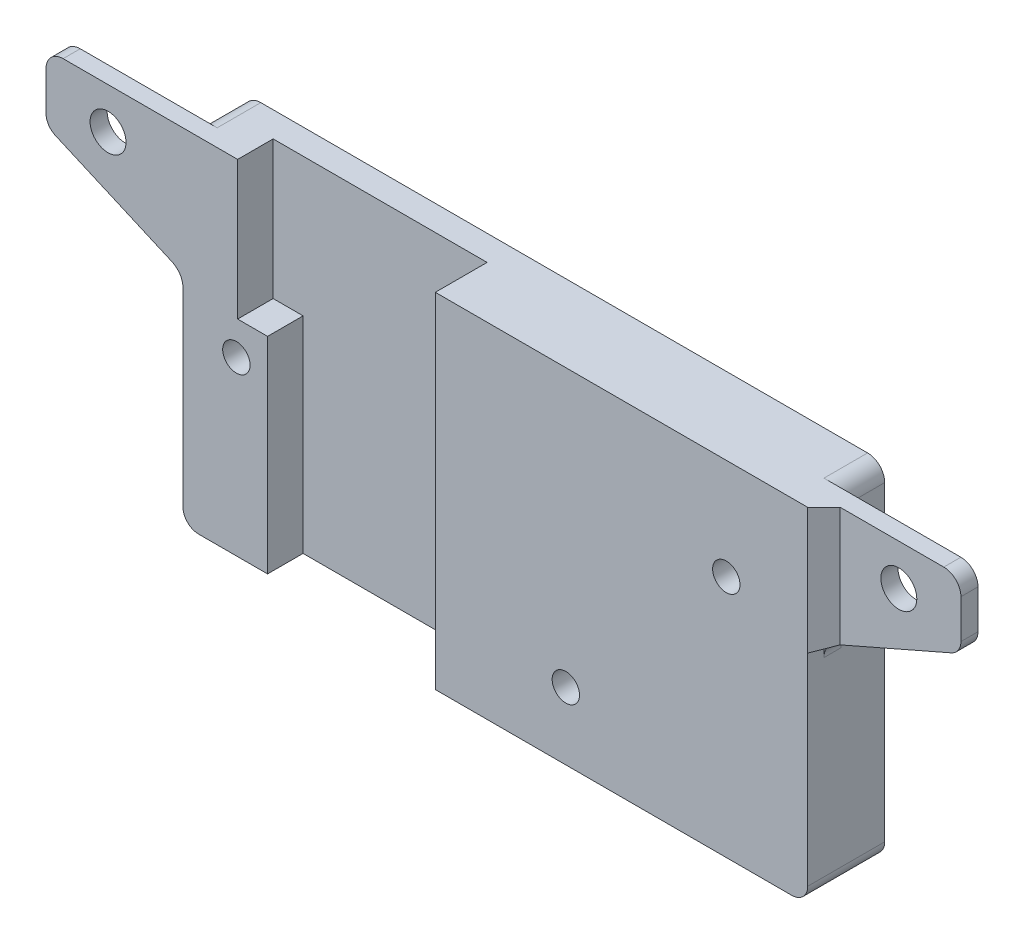
SolidWorks part; units mm, degrees
ref_plane "Front Plane" through (0, 0, 0) normal (0, 0, 1) x (1, 0, 0)
ref_plane "Top Plane" through (0, 0, 0) normal (0, 1, 0) x (1, 0, 0)
ref_plane "Right Plane" through (0, 0, 0) normal (1, 0, 0) x (0, 0, -1)
sketch "Sketch1" plane through (0, 0, 0) normal (0, 0, 1) x (1, 0, 0)
  line L0 (99.95, 149.85) -> (25.05, 149.85)
  line L1 (25.05, 148) -> (25.05, 111.5)
  line L2 (26.9, 109.65) -> (98.1, 109.65)
  line L3 (99.95, 111.5) -> (99.95, 148)
  line L4 (24.9, 148) -> (24.9, 111.5)
  line L5 (26.9, 109.5) -> (98.1, 109.5)
  line L6 (100.1, 111.5) -> (100.1, 148)
  line L7 (102.1, 150) -> (22.9, 150)
  line L8 (24.9, 148) -> (24.9, 111.5) construction
  line L9 (26.9, 109.5) -> (98.1, 109.5) construction
  line L10 (100.1, 111.5) -> (100.1, 148) construction
  line L11 (102.1, 150) -> (22.9, 150) construction
  line L12 (25.05, 148) -> (25.05, 149.85)
  line L14 (101.0046, 149.85) -> (23.9954, 149.85) construction
  line L15 (99.95, 148) -> (99.95, 149.85)
  arc A1 (25.05, 111.5) -> (26.9, 109.65) centre (26.9, 111.5) ccw
  arc A2 (98.1, 109.65) -> (99.95, 111.5) centre (98.1, 111.5) ccw
  arc A4 (24.9, 111.5) -> (26.9, 109.5) centre (26.9, 111.5) ccw
  arc A5 (98.1, 109.5) -> (100.1, 111.5) centre (98.1, 111.5) ccw
  arc A6 (102.1, 150) -> (100.1, 148) centre (102.1, 148) ccw
  arc A7 (24.9, 148) -> (22.9, 150) centre (22.9, 148) ccw
  arc A8 (24.9, 111.5) -> (26.9, 109.5) centre (26.9, 111.5) ccw construction
  arc A9 (98.1, 109.5) -> (100.1, 111.5) centre (98.1, 111.5) ccw construction
  arc A10 (102.1, 150) -> (100.1, 148) centre (102.1, 148) ccw construction
  arc A11 (24.9, 148) -> (22.9, 150) centre (22.9, 148) ccw construction
  arc A16 (25.05, 148) -> (23.9954, 149.85) centre (22.9, 148) ccw construction
  arc A17 (101.0046, 149.85) -> (99.95, 148) centre (102.1, 148) ccw construction
  dimension "D1" = 0
  dimension "D2" = 0.15
extrude "Boss-Extrude1" add sketch "Sketch1" along normal up to surface (5.1 mm away)
sketch "Sketch2" plane through (0, 0, 5.1) normal (0, 0, 1) x (1, 0, 0)
  line L24 (101.2984, 135.5243) -> (114.9016, 141.4757) construction
  line L25 (116.1, 143.308) -> (116.1, 148) construction
  line L26 (118.1, 150) -> (102.1, 150) construction
  line L28 (8.9, 148) -> (8.9, 143.308) construction
  line L29 (10.0984, 141.4757) -> (23.7016, 135.5243) construction
  line L31 (22.9, 150) -> (6.9, 150) construction
  line L32 (101.2984, 135.5243) -> (114.9016, 141.4757) construction
  line L33 (116.1, 143.308) -> (116.1, 148) construction
  line L34 (116.1, 150) -> (102.1, 150) construction
  line L36 (8.9, 148) -> (8.9, 143.308) construction
  line L37 (10.0984, 141.4757) -> (23.7016, 135.5243) construction
  line L39 (22.9, 150) -> (8.9, 150) construction
  line L40 (100.1, 111.5) -> (100.1, 133.692) construction
  line L41 (26.9, 109.5) -> (98.1, 109.5) construction
  line L42 (24.9, 133.692) -> (24.9, 111.5) construction
  line L43 (100.1, 111.5) -> (100.1, 133.692) construction
  line L44 (26.9, 109.5) -> (98.1, 109.5) construction
  line L45 (24.9, 133.692) -> (24.9, 111.5) construction
  line L46 (102.1, 150) -> (22.9, 150) construction
  line L47 (102.1, 150) -> (22.9, 150) construction
  line L48 (8.9, 148) -> (8.9, 150) construction
  line L49 (116.1, 148) -> (116.1, 150) construction
  line L50 (102.1, 149.85) -> (22.9, 149.85)
  line L51 (22.9, 149.85) -> (9.05, 149.85)
  line L52 (9.05, 148) -> (9.05, 149.85)
  line L53 (9.05, 148) -> (9.05, 143.308)
  line L54 (10.1585, 141.6131) -> (23.7618, 135.6617)
  line L55 (25.05, 133.692) -> (25.05, 111.5)
  line L56 (26.9, 109.65) -> (98.1, 109.65)
  line L57 (99.95, 111.5) -> (99.95, 133.692)
  line L58 (101.2382, 135.6617) -> (114.8415, 141.6131)
  line L59 (115.95, 143.308) -> (115.95, 148)
  line L60 (115.95, 148) -> (115.95, 149.85)
  line L61 (115.95, 149.85) -> (102.1, 149.85)
  arc A24 (114.9016, 141.4757) -> (116.1, 143.308) centre (114.1, 143.308) ccw construction
  arc A27 (101.2984, 135.5243) -> (100.1, 133.692) centre (102.1, 133.692) ccw construction
  arc A28 (8.9, 143.308) -> (10.0984, 141.4757) centre (10.9, 143.308) ccw construction
  arc A29 (24.9, 133.692) -> (23.7016, 135.5243) centre (22.9, 133.692) ccw construction
  arc A32 (114.9016, 141.4757) -> (116.1, 143.308) centre (114.1, 143.308) ccw construction
  arc A35 (101.2984, 135.5243) -> (100.1, 133.692) centre (102.1, 133.692) ccw construction
  arc A36 (8.9, 143.308) -> (10.0984, 141.4757) centre (10.9, 143.308) ccw construction
  arc A37 (24.9, 133.692) -> (23.7016, 135.5243) centre (22.9, 133.692) ccw construction
  arc A40 (98.1, 109.5) -> (100.1, 111.5) centre (98.1, 111.5) ccw construction
  arc A41 (24.9, 111.5) -> (26.9, 109.5) centre (26.9, 111.5) ccw construction
  arc A42 (98.1, 109.5) -> (100.1, 111.5) centre (98.1, 111.5) ccw construction
  arc A43 (24.9, 111.5) -> (26.9, 109.5) centre (26.9, 111.5) ccw construction
  arc A44 (9.05, 143.308) -> (10.1585, 141.6131) centre (10.9, 143.308) ccw
  arc A45 (25.05, 133.692) -> (23.7618, 135.6617) centre (22.9, 133.692) ccw
  arc A46 (25.05, 111.5) -> (26.9, 109.65) centre (26.9, 111.5) ccw
  arc A47 (98.1, 109.65) -> (99.95, 111.5) centre (98.1, 111.5) ccw
  arc A48 (101.2382, 135.6617) -> (99.95, 133.692) centre (102.1, 133.692) ccw
  arc A49 (114.8415, 141.6131) -> (115.95, 143.308) centre (114.1, 143.308) ccw
  circle A50 centre (16.3, 145.05) radius 2.1
  circle A51 centre (108.7, 145.05) radius 2.1
  dimension "D2" = 4.2
  dimension "D1" = 0.15
extrude "Boss-Extrude2" add sketch "Sketch2" along normal up to surface (0.9 mm away)
fillet "Fillet1" radius 2 4 edges at (115.95, 149.85, 5.55) (9.05, 149.85, 5.55) (25.05, 149.85, 2.55) (99.95, 149.85, 2.55)
sketch "Sketch3" plane through (0, 0, 6) normal (0, 0, 1) x (1, 0, 0)
  line L0 (99.95, 133.692) -> (99.95, 149.85)
  line L1 (11.05, 149.85) -> (113.95, 149.85) construction
  line L2 (114.8415, 141.6131) -> (101.2382, 135.6617) construction
  line L3 (115.95, 147.85) -> (115.95, 143.308) construction
  line L4 (114.8415, 141.6131) -> (101.2382, 135.6617)
  line L5 (115.95, 147.85) -> (115.95, 143.308)
  line L6 (11.05, 149.85) -> (25.05, 149.85)
  line L7 (25.05, 133.692) -> (25.05, 149.85)
  line L8 (23.7618, 135.6617) -> (10.1585, 141.6131) construction
  line L9 (9.05, 143.308) -> (9.05, 147.85) construction
  line L10 (23.7618, 135.6617) -> (10.1585, 141.6131)
  line L11 (9.05, 143.308) -> (9.05, 147.85)
  line L12 (99.95, 149.85) -> (113.95, 149.85)
  arc A0 (101.2382, 135.6617) -> (99.95, 133.692) centre (102.1, 133.692) ccw construction
  arc A1 (114.8415, 141.6131) -> (115.95, 143.308) centre (114.1, 143.308) ccw construction
  arc A2 (115.95, 147.85) -> (113.95, 149.85) centre (113.95, 147.85) ccw construction
  arc A3 (101.2382, 135.6617) -> (99.95, 133.692) centre (102.1, 133.692) ccw
  arc A4 (114.8415, 141.6131) -> (115.95, 143.308) centre (114.1, 143.308) ccw
  arc A5 (115.95, 147.85) -> (113.95, 149.85) centre (113.95, 147.85) ccw
  arc A6 (25.05, 133.692) -> (23.7618, 135.6617) centre (22.9, 133.692) ccw construction
  arc A7 (9.05, 143.308) -> (10.1585, 141.6131) centre (10.9, 143.308) ccw construction
  arc A8 (11.05, 149.85) -> (9.05, 147.85) centre (11.05, 147.85) ccw construction
  arc A9 (25.05, 133.692) -> (23.7618, 135.6617) centre (22.9, 133.692) ccw
  arc A10 (9.05, 143.308) -> (10.1585, 141.6131) centre (10.9, 143.308) ccw
  arc A11 (11.05, 149.85) -> (9.05, 147.85) centre (11.05, 147.85) ccw
  circle A12 centre (108.7, 145.05) radius 2.1 construction
  circle A13 centre (16.3, 145.05) radius 2.1 construction
  circle A14 centre (108.7, 145.05) radius 2.1
  circle A15 centre (16.3, 145.05) radius 2.1
extrude "Boss-Extrude3" add sketch "Sketch3" along normal offset from surface (1.1 mm away) 2 up to face at (17.4291, 143.8163, 5.1)
sketch "Sketch4" plane through (0, 149.85, 0) normal (0, 1, 0) x (1, 0, 0)
  line L0 (99.95, -7.1) -> (97.45, -6)
  line L1 (25.05, -6) -> (99.95, -6) construction
  line L2 (97.45, -6) -> (99.95, -6)
  line L3 (25.05, -6) -> (25.05, -7.1)
  line L4 (25.05, -7.1) -> (27.55, -6)
  line L5 (27.55, -6) -> (25.05, -6)
  line M6 (25.05, -7.1) -> (25.05, -6)
  line M7 (25.05, -6) -> (99.95, -6)
  line M8 (99.95, -6) -> (99.95, -7.1)
  dimension "D1" = 2.5
extrude "Boss-Extrude4" add sketch "Sketch4" against normal up to vertex (16.158 mm away) contours L4 M6 M7 | L0 M8 M7 up to point (25.05, 133.692, 7.1)
sketch "Sketch5" plane through (0, 0, 6) normal (0, 0, 1) x (1, 0, 0)
  line L0 (27.55, 149.85) -> (97.45, 149.85) construction
  line L1 (31.44, 149.85) -> (56.44, 149.85)
  line L2 (31.44, 149.85) -> (31.44, 109.65)
  line L3 (31.44, 109.65) -> (56.44, 109.65)
  line L4 (56.44, 149.85) -> (56.44, 109.65)
  line L5 (98.1, 109.65) -> (26.9, 109.65) construction
  line L6 (27.55, 133.692) -> (27.55, 149.85) construction
  dimension "D1" = 3.89
  dimension "D2" = 25
extrude "Cut-Extrude2" cut sketch "Sketch5" against normal blind 3.05
sketch "Sketch6" plane through (31.44, 0, 0) normal (1, 0, 0) x (0, 0, -1)
  line L0 (0, 149.85) -> (0, 109.65) construction
  line L1 (-6, 109.65) -> (0, 109.65)
  line L2 (-6, 109.65) -> (-6, 133.85)
  line L3 (-6, 133.85) -> (0, 133.85)
  line L4 (0, 109.65) -> (0, 133.85)
  line L5 (-2.95, 149.85) -> (-6, 149.85) construction
  dimension "D1" = 16
extrude "Boss-Extrude5" add sketch "Sketch6" along normal blind 3.5
sketch "Sketch9" plane through (0, 133.692, 0) normal (0, -1, 0) x (1, 0, 0)
  line L0 (97.45, 6) -> (99.95, 7.1)
  line L1 (99.95, 7.1) -> (99.95, 6) construction
  line L2 (99.95, 7.1) -> (97.45, 6) construction
  line L3 (99.95, 7.1) -> (99.95, 6)
  line L4 (99.95, 6) -> (97.45, 6)
extrude "Cut-Extrude3" cut sketch "Sketch9" against normal up to surface (16.158 mm away) up to face at (57.86, 149.85, 4.9188)
sketch "Sketch10" plane through (0, 0, 6) normal (0, 0, 1) x (1, 0, 0)
  line L0 (56.44, 149.85) -> (56.44, 109.65)
  line L1 (56.44, 109.65) -> (98.1, 109.65)
  line L2 (56.44, 149.85) -> (99.95, 149.85)
  line L3 (99.95, 149.85) -> (99.95, 111.5)
  arc A0 (99.95, 111.5) -> (98.1, 109.65) centre (98.1, 111.5) cw
extrude "Boss-Extrude6" add sketch "Sketch10" along normal blind 3
sketch "Sketch12" plane through (0, 149.85, 0) normal (0, 1, 0) x (1, 0, 0)
  line L0 (99.95, -9) -> (99.95, -7.1)
  line L1 (99.95, -9) -> (99.95, -7.1) construction
  line L2 (99.95, -7.1) -> (101.85, -7.1)
  line L3 (113.95, -7.1) -> (99.95, -7.1) construction
  line L4 (101.85, -7.1) -> (99.95, -9)
  dimension "D1" = 1.9
  dimension "D2" = 1.9
extrude "Boss-Extrude7" add sketch "Sketch12" against normal up to surface (13.9206 mm away)
sketch "Sketch15" plane through (0, 0, 7.1) normal (0, 0, 1) x (1, 0, 0)
  line L2 (101.2382, 135.6617) -> (99.95, 135.0981)
  line L3 (99.95, 135.0981) -> (99.95, 133.692)
  arc A1 (101.2382, 135.6617) -> (99.95, 133.692) centre (102.1, 133.692) ccw
sketch "Sketch21" plane through (0, 0, 9) normal (0, 0, 1) x (1, 0, 0)
  line L0 (99.95, 149.85) -> (56.44, 149.85) construction
  line L1 (99.95, 135.0981) -> (99.95, 149.85) construction
  line L2 (56.44, 109.65) -> (98.1, 109.65) construction
  line L3 (99.95, 111.5) -> (99.95, 135.0981) construction
  circle A0 centre (90.44, 138.06) radius 1.6
  circle A1 centre (71.69, 117.51) radius 1.6
  dimension "D1" = 3.2
  dimension "D2" = 3.2
  dimension "D4" = 9.51
  dimension "D5" = 7.86
  dimension "D6" = 28.26
  dimension "D3" = 11.79
extrude "Cut-Extrude6" cut sketch "Sketch21" against normal up to surface (9 mm away) up to face at (62.5, 129.7203, 0)
sketch "Sketch22" plane through (0, 133.692, 0) normal (0, -1, 0) x (1, 0, 0)
  line L0 (25.05, 7.1) -> (25.05, 6)
  line L1 (25.05, 6) -> (27.55, 6)
  line L2 (27.55, 6) -> (25.05, 7.1)
extrude "Cut-Extrude7" cut sketch "Sketch22" against normal through all
sketch "Sketch23" plane through (25.05, 0, 0) normal (1, 0, 0) x (0, 0, -1)
  line L7 (-6, 149.85) -> (-7.1, 149.85)
  line L8 (-6, 149.85) -> (-6, 133.692)
  line L9 (-6, 133.692) -> (-7.1, 133.692)
  line L10 (-7.1, 149.85) -> (-7.1, 133.692)
extrude "Boss-Extrude9" add sketch "Sketch23" along normal up to surface (6.39 mm away) contours L8 L9 L10 L7 up to face at (31.44, 141.85, 4.475)
sketch "Sketch26" plane through (0, 133.85, 0) normal (0, 1, 0) x (1, 0, 0)
  line L1 (31.44, -2.95) -> (34.94, -2.95)
  line L2 (31.44, -2.95) -> (31.44, -6)
  line L3 (31.44, -6) -> (34.94, -6)
  line L4 (34.94, -2.95) -> (34.94, -6)
extrude "Cut-Extrude11" cut sketch "Sketch26" against normal up to surface (0.158 mm away) up to face at (28.245, 133.692, 6.55)
sketch "Sketch27" plane through (0, 0, 6) normal (0, 0, 1) x (1, 0, 0)
  line L0 (34.94, 109.65) -> (34.94, 133.692)
  line L1 (34.94, 133.692) -> (25.05, 133.692)
  line L2 (25.05, 133.692) -> (25.05, 111.5)
  line L3 (34.94, 109.65) -> (26.9, 109.65)
  arc A0 (26.9, 109.65) -> (25.05, 111.5) centre (26.9, 111.5) cw
extrude "Boss-Extrude10" add sketch "Sketch27" along normal up to surface (1.1 mm away) up to face at (18.4, 145.05, 7.1)
sketch "Sketch28" plane through (0, 0, 7.1) normal (0, 0, 1) x (1, 0, 0)
  line L1 (34.94, 109.65) -> (34.94, 133.692) construction
  line L2 (31.44, 149.85) -> (11.05, 149.85) construction
  circle A0 centre (31.295, 129.75) radius 1.6
  dimension "D1" = 3.2
  dimension "D3" = 3.645
  dimension "D2" = 20.1
extrude "Cut-Extrude12" cut sketch "Sketch28" against normal up to surface (7.1 mm away) contours A0 up to face at (92.04, 138.06, 0)
equation "\"width\"= 24"
equation "\"thk\"= 3"
equation "\"holesize\"= 4.2"
equation "\"holedistance\"= ( 20 + 12 ) / 2"
equation "\"threaded_hole\"= 3.9"
equation "\"fillet_radius\"= 2"
equation "\"ground_clearance\"= 25"
equation "\"tire_thk\"= 3"
equation "\"innerwheel_diam\" = \"wheel_diam\"-2*\"tire_thk\""
equation "\"innerwheel_thk\"= 8"
equation "\"wheel_diam\"= 2*(\"width\"/2+\"ground_clearance\")"
equation "\"coloursensor_holesize\"= 2.65"
equation "\"hole_to_edge\" = 4"
equation "\"M4_insert_diam\"= 5.7"
